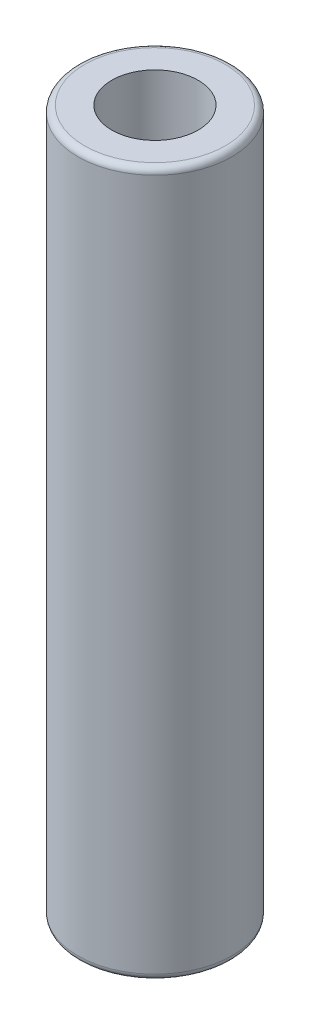
SolidWorks part; units mm, degrees
material "Chrome Stainless Steel"
ref_plane "Front" through (0, 0, 0) normal (0, 0, 1) x (1, 0, 0)
ref_plane "Top" through (0, 0, 0) normal (0, 1, 0) x (1, 0, 0)
ref_plane "Right" through (0, 0, 0) normal (1, 0, 0) x (0, 0, -1)
sketch "Sketch1" plane through (0, 0, 0) normal (0, 0, 1) x (1, 0, 0)
  line L0 (0, 288.3922) -> (0, -278.7099) construction
  line L1 (-369.3079, 0) -> (390.0556, 0) construction
  line L2 (0, 0) -> (0, 87.3506)
  line L3 (0, 87.3506) -> (8.7313, 87.3506)
  line L4 (9.525, 86.5568) -> (9.525, 0.7938)
  line L5 (8.7313, 0) -> (0, 0)
  arc A0 (9.525, 86.5568) -> (8.7313, 87.3506) centre (8.7313, 86.5569) ccw
  arc A1 (8.7313, 0) -> (9.525, 0.7938) centre (8.7313, 0.7937) ccw
  point P13 (9.525, 0)
  dimension "D3" = 0.7937
  dimension "D4" = 0.7937
  dimension "D1" = 87.3506
  dimension "D2" = 19.05
revolve "Revolve1" add sketch "Sketch1" angle 360 about L0
hole_wizard "1/2-13 Tapped Hole1" positions "Sketch2" profile "Sketch3" tap size "1/2-13" standard "ANSI Inch"
sketch "Sketch2" plane through (0, 87.3506, 0) normal (0, 1, 0) x (1, 0, 0)
  point P0 (0, 0)
sketch "Sketch3" plane through (0, 87.3506, 0) normal (1, 0, 0) x (0, 0, 1)
  line L0 (0, 0) -> (0, 22.2695)
  line L1 (0, 22.2695) -> (5.3581, 19.05)
  line L2 (5.3581, 19.05) -> (5.3581, 0)
  line L5 (5.3581, 0) -> (0, 0)
  line L10 (0, 22.2695) -> (-5.3581, 19.05) construction
  line L11 (0, -6.35) -> (0, 107.95) construction
  dimension "Tap Drill Dia." = 10.7163
  dimension "Tap Drill Depth" = 19.05
  dimension "Drill Angle" = 118
cosmetic thread "Hole Thread1"
